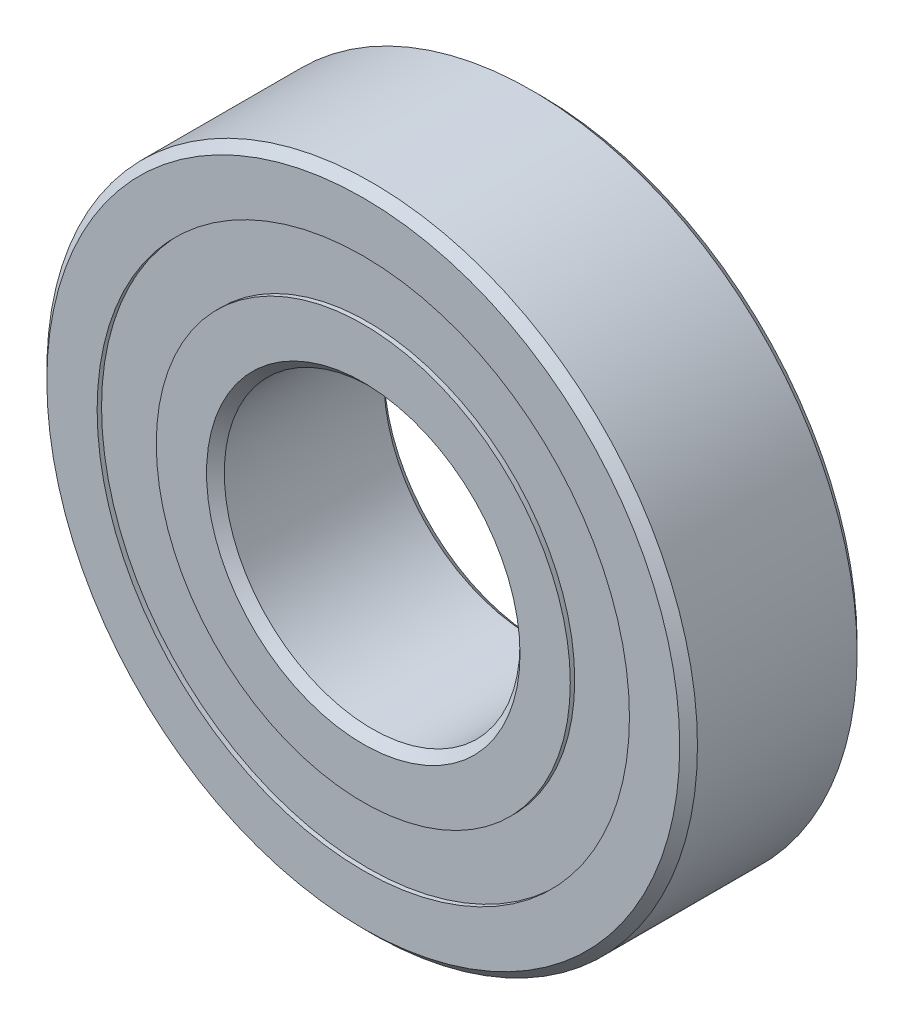
SolidWorks part; units mm, degrees
ref_plane "Front Plane" through (0, 0, 0) normal (0, 0, 1) x (1, 0, 0)
ref_plane "Top Plane" through (0, 0, 0) normal (0, 1, 0) x (1, 0, 0)
ref_plane "Right Plane" through (0, 0, 0) normal (1, 0, 0) x (0, 0, -1)
sketch "Sketch1" plane through (0, 0, 0) normal (0, 0, 1) x (1, 0, 0)
  circle A0 centre (0, 0) radius 11 construction
  circle A1 centre (0, 0) radius 5 construction
  dimension "OD" = 22
  dimension "ID" = 10
sketch "Sketch2" plane through (0, 0, 0) normal (1, 0, 0) x (0, 0, -1)
  line L0 (-3, 0) -> (3, 0) construction
  line L1 (0, 11) -> (0, -11) construction
  line L2 (2.7, 11) -> (-2.7, 11) construction
  line L3 (-2.7, 11) -> (-3, 10.7) construction
  line L4 (-3, 10.7) -> (-3, 9) construction
  line L5 (-3, 9) -> (-1.3333, 9) construction
  line L6 (3, 9) -> (1.3333, 9) construction
  line L7 (3, 10.7) -> (3, 9) construction
  line L8 (2.7, 11) -> (3, 10.7) construction
  line L9 (0, 11) -> (0, 8) construction
  line L10 (0, 8) -> (0, 5) construction
  line L11 (3, 8) -> (-3, 8) construction
  line L12 (-3, 5.3) -> (-3, 7) construction
  line L13 (-2.7, 5) -> (-3, 5.3) construction
  line L14 (2.7, 5) -> (-2.7, 5) construction
  line L15 (2.7, 5) -> (3, 5.3) construction
  line L16 (3, 5.3) -> (3, 7) construction
  line L17 (3, 7) -> (1.3333, 7) construction
  line L18 (-3, 7) -> (-1.3333, 7) construction
  line L19 (-3, 5) -> (-3, -5) construction
  line L20 (3, 11) -> (3, -11) construction
  arc A0 (-1.3333, 9) -> (1.3333, 9) centre (0, 8) cw construction
  arc A1 (-1.3333, 7) -> (1.3333, 7) centre (0, 8) ccw construction
  point P14 (0, 5)
  point P18 (0, 8)
  dimension "Approx. Ball Dia." = 3.3333
  dimension "D1" = 45
  dimension "D2" = 0.3
  dimension "D3" = 2.6667
  dimension "D4" = 1
  dimension "Width" = 6
  dimension "For Shaft Diameter" = 10
  dimension "For Housing ID" = 22
sketch "Sketch3" plane through (0, 0, 0) normal (1, 0, 0) x (0, 0, -1)
  line L0 (-3, 10.7) -> (-3, 9) construction
  line L1 (-2.7, 11) -> (-3, 10.7) construction
  line L2 (2.7, 11) -> (-2.7, 11) construction
  line L3 (2.7, 11) -> (3, 10.7) construction
  line L4 (3, 10.7) -> (3, 9) construction
  line L5 (3, 9) -> (1.3333, 9) construction
  line L6 (-3, 9) -> (-1.3333, 9) construction
  line L7 (-3, 10.7) -> (-3, 9)
  line L8 (-2.7, 11) -> (-3, 10.7)
  line L9 (2.7, 11) -> (-2.7, 11)
  line L10 (2.7, 11) -> (3, 10.7)
  line L11 (3, 10.7) -> (3, 9)
  line L12 (3, 9) -> (1.3333, 9)
  line L13 (-3, 9) -> (-1.3333, 9)
  line L14 (-3, 5.3) -> (-3, 7) construction
  line L15 (-2.7, 5) -> (-3, 5.3) construction
  line L16 (2.7, 5) -> (-2.7, 5) construction
  line L17 (2.7, 5) -> (3, 5.3) construction
  line L18 (3, 5.3) -> (3, 7) construction
  line L19 (3, 7) -> (1.3333, 7) construction
  line L20 (-3, 7) -> (-1.3333, 7) construction
  line L21 (-3, 5.3) -> (-3, 7)
  line L22 (-2.7, 5) -> (-3, 5.3)
  line L23 (2.7, 5) -> (-2.7, 5)
  line L24 (2.7, 5) -> (3, 5.3)
  line L25 (3, 5.3) -> (3, 7)
  line L26 (3, 7) -> (1.3333, 7)
  line L27 (-3, 7) -> (-1.3333, 7)
  arc A0 (1.3333, 9) -> (-1.3333, 9) centre (0, 8) ccw construction
  arc A1 (1.3333, 9) -> (-1.3333, 9) centre (0, 8) ccw
  arc A2 (-1.3333, 7) -> (1.3333, 7) centre (0, 8) ccw construction
  arc A3 (-1.3333, 7) -> (1.3333, 7) centre (0, 8) ccw
revolve "Revolve1" add sketch "Sketch3" angle 360 about L0
sketch "Sketch4" plane through (0, 0, 0) normal (1, 0, 0) x (0, 0, -1)
  line L0 (-1.6667, 8) -> (1.6667, 8)
  arc A2 (-1.6667, 8) -> (1.6667, 8) centre (0, 8) cw
  arc A3 (1.3333, 9) -> (-1.3333, 9) centre (0, 8) ccw construction
revolve "Revolve2" add sketch "Sketch4" angle 360 about L0
pattern_circular "CirPattern1" count 10 over 360 about axis through (0, 0, 0) along (0, 0, 1) of bodies 104
sketch "Sketch5" plane through (0, 0, 0) normal (1, 0, 0) x (0, 0, -1)
  line L0 (-3, 9) -> (-1.3333, 9) construction
  line L1 (-2.85, 9) -> (-1.6667, 9)
  line L2 (-2.85, 9) -> (-2.85, 7)
  line L3 (-2.85, 7) -> (-1.6667, 7)
  line L4 (-1.6667, 9) -> (-1.6667, 7)
  line L6 (3, 9) -> (1.3333, 9) construction
  line L7 (2.85, 9) -> (1.6667, 9)
  line L8 (2.85, 9) -> (2.85, 7)
  line L9 (2.85, 7) -> (1.6667, 7)
  line L10 (1.6667, 9) -> (1.6667, 7)
  line L12 (-2.7, 11) -> (-3, 10.7) construction
  line L13 (-3, 7) -> (-1.3333, 7) construction
  line L14 (3, 7) -> (1.3333, 7) construction
  point P18 (-2.85, 10.85)
revolve "Revolve3" add sketch "Sketch5" angle 360 about L0
equation "\"D2@Sketch2\"= \"Width@Sketch2\" * .05"
equation "\"D3@Sketch2\"=\"Width@Sketch2\" / 2.25"
equation "\"D4@Sketch2\"=( \"OD@Sketch1\" - \"Width@Sketch2\" ) *.5 *.125"
equation "\"Approx. No. of Balls\"= ( pi * \"OD@Sketch1\" ) * .5 / \"Approx. Ball Dia.@Sketch2\""
equation "\"Balls@CirPattern1\"=\"Approx. No. of Balls\""
